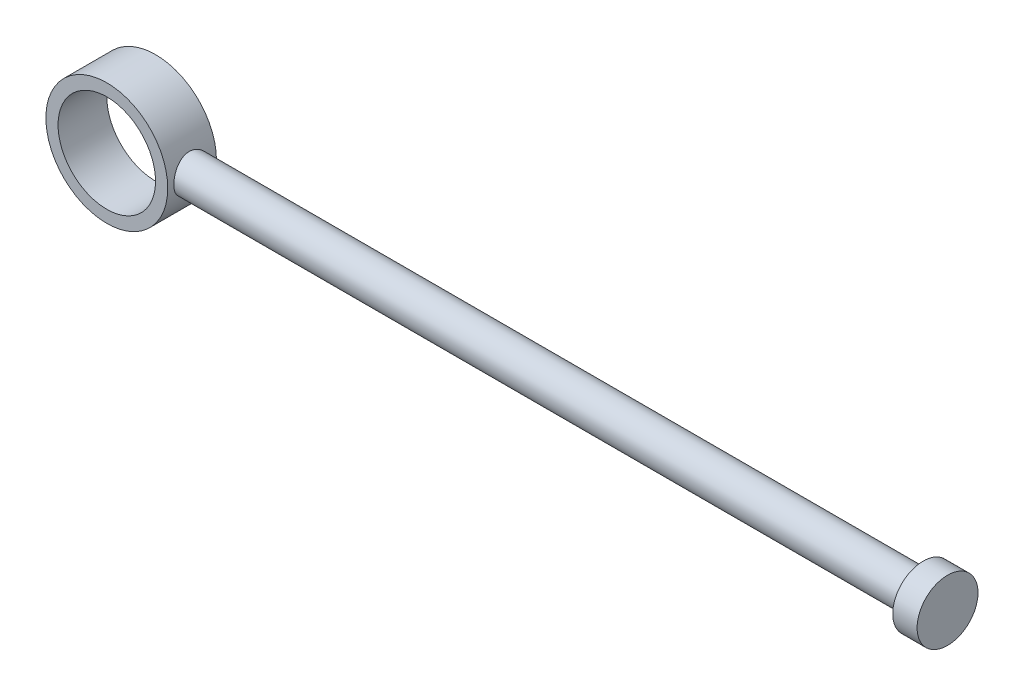
SolidWorks part; units mm, degrees
ref_plane "Ön Düzlem" through (0, 0, 0) normal (0, 0, 1) x (1, 0, 0)
ref_plane "Üst Düzlem" through (0, 0, 0) normal (0, 1, 0) x (1, 0, 0)
ref_plane "Sağ Düzlem" through (0, 0, 0) normal (1, 0, 0) x (0, 0, -1)
sketch "Çizim1" plane through (0, 0, 0) normal (0, 0, 1) x (1, 0, 0)
  circle A0 centre (0, 0) radius 4
  circle A1 centre (0, 0) radius 5
  dimension "D1" = 8
  dimension "D2" = 10
extrude "Yükseklik-Ekstrüzyon1" add sketch "Çizim1" along normal blind 4
ref_plane "Düzlem1" through (5, 0, 0) normal (1, 0, 0) x (0, 0, -1)
sketch "Çizim2" plane through (5, 0, 0) normal (1, 0, 0) x (0, 0, -1)
  line L0 (-2, 5) -> (-2, 0) construction
  line L1 (0, 5) -> (-4, 5) construction
  circle A0 centre (-2, 0) radius 1.5
  dimension "D1" = 3
  dimension "D2" = 2
extrude "Yükseklik-Ekstrüzyon2" add sketch "Çizim2" along normal blind 60 and the other way up to surface other way up to face at (5, 0, 4)
sketch "Çizim3" plane through (65, 0, 0) normal (1, 0, 0) x (0, 0, -1)
  circle A0 centre (-2, 0) radius 2.5
  dimension "D1" = 5
extrude "Yükseklik-Ekstrüzyon3" add sketch "Çizim3" along normal blind 2
